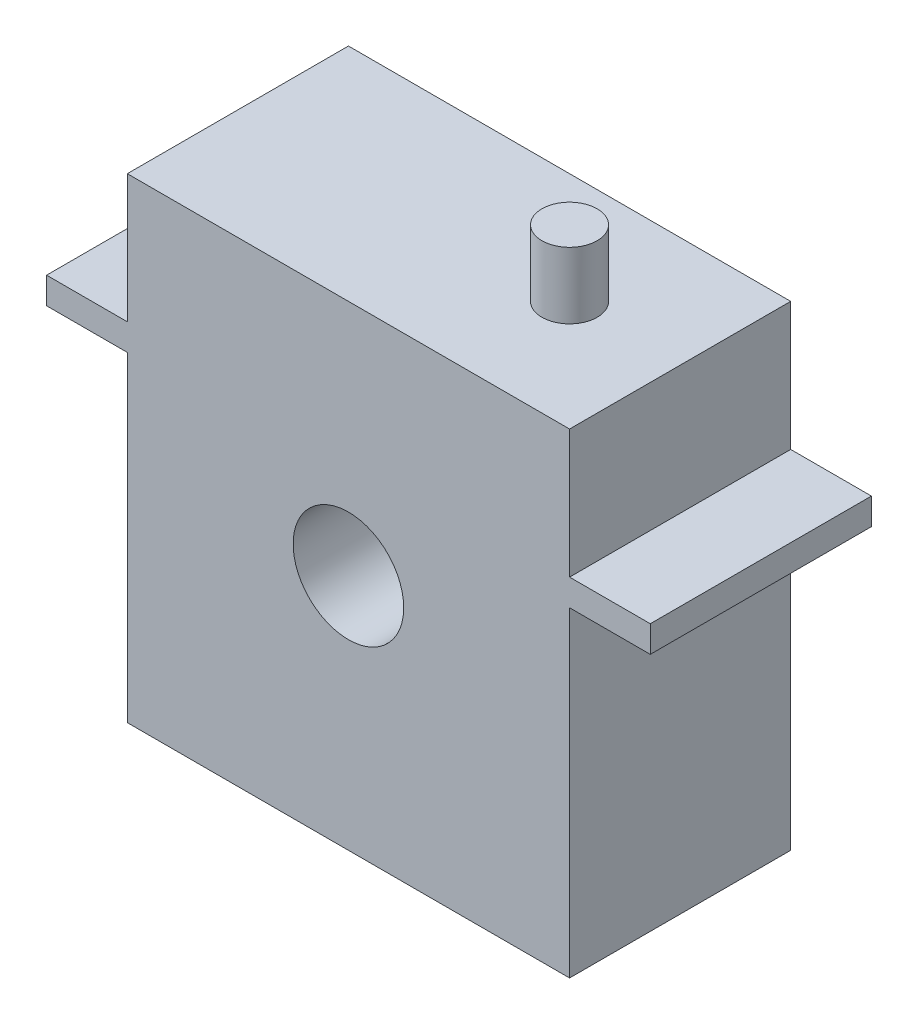
SolidWorks part; units mm, degrees
ref_plane "Front Plane" through (0, 0, 0) normal (0, 0, 1) x (1, 0, 0)
ref_plane "Top Plane" through (0, 0, 0) normal (0, 1, 0) x (1, 0, 0)
ref_plane "Right Plane" through (0, 0, 0) normal (1, 0, 0) x (0, 0, -1)
sketch "Sketch1" plane through (0, 0, 0) normal (0, 0, 1) x (1, 0, 0)
  line L1 (-20, -21.5) -> (20, -21.5)
  line L2 (-20, -21.5) -> (-20, 21.5)
  line L3 (-20, 21.5) -> (20, 21.5)
  line L4 (20, -21.5) -> (20, 21.5)
  line L5 (-20, -21.5) -> (20, 21.5) construction
  line L6 (-20, 21.5) -> (20, -21.5) construction
  circle A0 centre (0, 0) radius 5
  point P0 (0, 0)
  dimension "D2" = 10
  dimension "D1" = 40
  dimension "D3" = 43
extrude "Boss-Extrude1" add sketch "Sketch1" along normal blind 20
sketch "Sketch2" plane through (0, 21.5, 0) normal (0, 1, 0) x (1, 0, 0)
  line L0 (10, -10) -> (20, -10) construction
  line L1 (20, -20) -> (20, 0) construction
  line L2 (-20, -20) -> (-20, 0) construction
  circle A0 centre (10, -10) radius 2.5
  dimension "D1" = 5
  dimension "D2" = 10
extrude "Boss-Extrude2" add sketch "Sketch2" along normal blind 6
sketch "Sketch3" plane through (-20, 0, 0) normal (-1, 0, 0) x (0, 0, 1)
  line L0 (20, 21.5) -> (20, -21.5) construction
  line L1 (0, 7.5) -> (20, 7.5)
  line L2 (0, 7.5) -> (0, 9.9)
  line L3 (0, 9.9) -> (20, 9.9)
  line L4 (20, 7.5) -> (20, 9.9)
  line L5 (0, 7.5) -> (20, 9.9) construction
  line L6 (0, 9.9) -> (20, 7.5) construction
  line L7 (0, 21.5) -> (0, -21.5) construction
  line L8 (20, -21.5) -> (0, -21.5) construction
  point P0 (10, 8.7)
  dimension "D1" = 29
  dimension "D2" = 2.4
extrude "Boss-Extrude3" add sketch "Sketch3" along normal blind 7.3
mirror "Mirror1" about plane through (0, 0, 0) normal (1, 0, 0) of "Boss-Extrude3"
